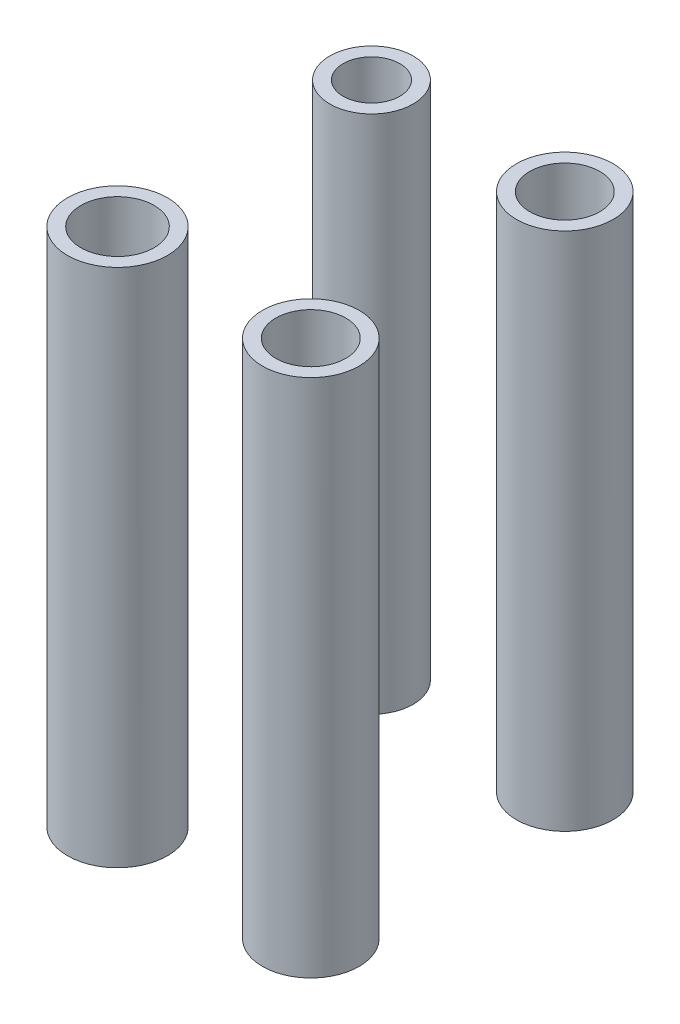
SolidWorks part; units mm, degrees
ref_plane "Alzado" through (0, 0, 0) normal (0, 0, 1) x (1, 0, 0)
ref_plane "Planta" through (0, 0, 0) normal (0, 1, 0) x (1, 0, 0)
ref_plane "Vista lateral" through (0, 0, 0) normal (1, 0, 0) x (0, 0, -1)
sketch "Croquis1" plane through (0, 0, 0) normal (0, 1, 0) x (1, 0, 0)
  line L0 (0, 37) -> (0, 32) construction
  line L1 (-24.5, 37) -> (24.5, 37)
  line L2 (-24.5, 37) -> (-24.5, -36)
  line L3 (-24.5, -36) -> (24.5, -36)
  line L4 (24.5, 37) -> (24.5, -36)
  line L5 (0, -29) -> (0, -36) construction
  line L6 (-6.25, -6.1) -> (-24.5, -6.1) construction
  line L7 (-14.5, -21.1) -> (14.5, -21.1) construction
  circle A0 centre (14.5, -21.1) radius 5.25
  circle A1 centre (-14.5, -21.1) radius 5.5
  circle A2 centre (-14.5, 17) radius 4.25
  circle A3 centre (14.5, 17) radius 5.25
  circle A6 centre (-19.5, 32) radius 3
  circle A7 centre (19.5, 32) radius 3
  point P0 (0, 0)
  point P10 (0, -17.55)
  dimension "D8" = 14.9
  dimension "D16" = 10.5
  dimension "D17" = 11
  dimension "D18" = 10
  dimension "D10" = 20
  dimension "D11" = 20
  dimension "D13" = 10
  dimension "D14" = 8.5
  dimension "D15" = 10.5
  dimension "D9" = 10
  dimension "D19" = 10
  dimension "D30" = 5
  dimension "D31" = 6
  dimension "D32" = 5
  dimension "D33" = 5
  dimension "D34" = 5
  dimension "D35" = 6
  dimension "D4" = 5
  dimension "D6" = 7
  dimension "D12" = 49
  dimension "D20" = 73
  dimension "D22" = 15
extrude "Saliente-Extruir4" add sketch "Croquis1" along normal blind 2
sketch "Croquis7" plane through (0, 2, 0) normal (0, 1, 0) x (1, 0, 0)
  line L1 (-24.5, -36) -> (24.5, -36)
  line L2 (-24.5, -36) -> (-24.5, -41)
  line L3 (-24.5, -41) -> (24.5, -41)
  line L4 (24.5, -36) -> (24.5, -41)
  dimension "D1" = 49
  dimension "D2" = 5
extrude "Saliente-Extruir5" add sketch "Croquis7" against normal up to surface (2 mm away) up to face at (0, 0, -0.5)
sketch "Croquis8" plane through (0, 2, 0) normal (0, 1, 0) x (1, 0, 0)
  line L0 (-19.5, -36) -> (19.5, -36) construction
  line L1 (-24.5, -41) -> (24.5, -41) construction
  line L2 (24.5, -41) -> (24.5, 37) construction
  line L3 (-24.5, 37) -> (-24.5, -41) construction
  circle A0 centre (-19.5, -36) radius 3
  circle A1 centre (19.5, -36) radius 3
  dimension "D2" = 5
  dimension "D3" = 6
  dimension "D4" = 5
  dimension "D5" = 6
  dimension "D1" = 5
extrude "Cortar-Extruir2" cut sketch "Croquis8" against normal blind 10
sketch "Croquis9" plane through (0, 2, 0) normal (0, 1, 0) x (1, 0, 0)
  circle A0 centre (-14.5, 17) radius 4.25
  circle A1 centre (-14.5, 17) radius 6.25
  dimension "D1" = 8.5
  dimension "D2" = 2
extrude "Saliente-Extruir6" add sketch "Croquis9" against normal blind 80
sketch "Croquis10" plane through (0, 2, 0) normal (0, 1, 0) x (1, 0, 0)
  circle A0 centre (14.5, 17) radius 5.25
  circle A1 centre (14.5, 17) radius 7.25
  dimension "D1" = 10.5
  dimension "D2" = 2
extrude "Saliente-Extruir7" add sketch "Croquis10" against normal blind 80
sketch "Croquis11" plane through (0, 2, 0) normal (0, 1, 0) x (1, 0, 0)
  circle A0 centre (-14.5, -21.1) radius 5.5
  circle A1 centre (-14.5, -21.1) radius 7.5
  circle A2 centre (14.5, -21.1) radius 5.25
  circle A3 centre (14.5, -21.1) radius 7.25
  dimension "D1" = 10.5
  dimension "D2" = 11
  dimension "D3" = 2
  dimension "D4" = 2
extrude "Saliente-Extruir8" add sketch "Croquis11" against normal blind 80
sketch "Croquis12" plane through (0, 0, -37) normal (0, 0, -1) x (-1, 0, 0)
  line L1 (-24.5, 0) -> (25.3676, 0)
  line L2 (-24.5, 0) -> (-24.5, 5.7001)
  line L3 (-24.5, 5.7001) -> (25.3676, 5.7001)
  line L4 (25.3676, 0) -> (25.3676, 5.7001)
extrude "Cortar-Extruir3" cut sketch "Croquis12" against normal through all
